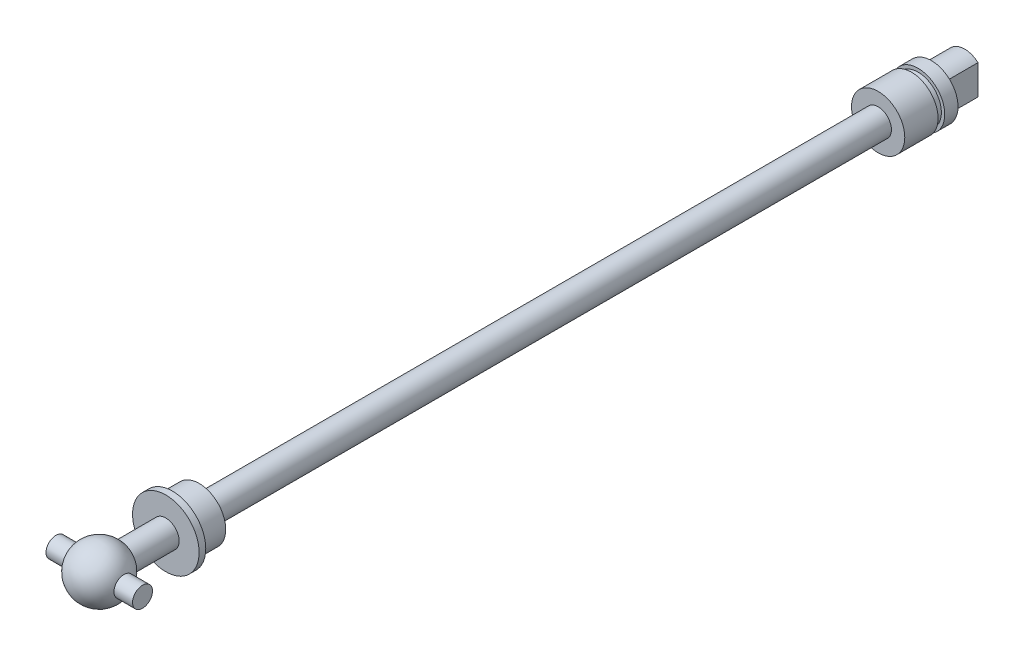
SolidWorks part; units mm, degrees
material "AISI 1020"
ref_plane "Front Plane" through (0, 0, 0) normal (0, 0, 1) x (1, 0, 0)
ref_plane "Top Plane" through (0, 0, 0) normal (0, 1, 0) x (1, 0, 0)
ref_plane "Right Plane" through (0, 0, 0) normal (1, 0, 0) x (0, 0, -1)
sketch "Sketch1" plane through (0, 0, 0) normal (1, 0, 0) x (0, 0, -1)
  line L0 (0, 0) -> (134, 0) construction
  line L1 (7.4641, 2) -> (14, 2)
  line L2 (14, 2) -> (14, 5)
  line L3 (14, 5) -> (15, 5)
  line L4 (15, 5) -> (15, 4)
  line L5 (15, 4) -> (19, 4)
  line L6 (19, 4) -> (19, 2)
  line L7 (19, 2) -> (121, 2)
  line L8 (121, 2) -> (121, 4)
  line L9 (121, 4) -> (126, 4)
  line L10 (126, 4) -> (126, 3.5)
  line L11 (126, 3.5) -> (127, 3.5)
  line L12 (127, 3.5) -> (127, 4)
  line L13 (127, 4) -> (129, 4)
  line L14 (129, 4) -> (129, 3)
  line L15 (129, 3) -> (134, 3)
  line L16 (134, 3) -> (134, 0)
  line L17 (0, 0) -> (134, 0)
  arc A0 (7.4641, 2) -> (0, 0) centre (4, 0) ccw
  dimension "D2" = 8
  dimension "D1" = 134
  dimension "D3" = 10
  dimension "D4" = 2
  dimension "D5" = 2
  dimension "D6" = 4
  dimension "D7" = 5
  dimension "D8" = 4
  dimension "D9" = 4
  dimension "D10" = 3
  dimension "D11" = 3.5
  dimension "D12" = 1
  dimension "D13" = 4
  dimension "D15" = 5
  dimension "D16" = 3
  dimension "D17" = 1
  dimension "D18" = 5
revolve "Revolve1" add sketch "Sketch1" angle 360 about L0
sketch "Sketch2" plane through (0, 0, -134) normal (0, 0, -1) x (-1, 0, 0)
  line L0 (0, -3) -> (0, 3) construction
  line L1 (2, -2.2361) -> (2, 2.2361)
  line L2 (-2, -2.2361) -> (-2, 2.2361)
  line L3 (-2, -3) -> (-2, 3) construction
  line L4 (2, -3) -> (2, 3) construction
  circle A2 centre (0, 0) radius 3
  circle A3 centre (0, 0) radius 3
  circle M3 centre (0, 0) radius 3
  dimension "D1" = 0
  dimension "D2" = 2
  dimension "D3" = 2
extrude "Cut-Extrude1" cut sketch "Sketch2" against normal up to surface (5 mm away) contours L2 M3 | L1 M3 up to face at (4, 0, -129)
sketch "Sketch3" plane through (0, 0, 0) normal (1, 0, 0) x (0, 0, -1)
  circle A0 centre (4, 0) radius 4
  circle A1 centre (4, 0) radius 1.5
  dimension "D2" = 3
extrude "Boss-Extrude1" add sketch "Sketch3" along normal mid plane 13 contours A1
